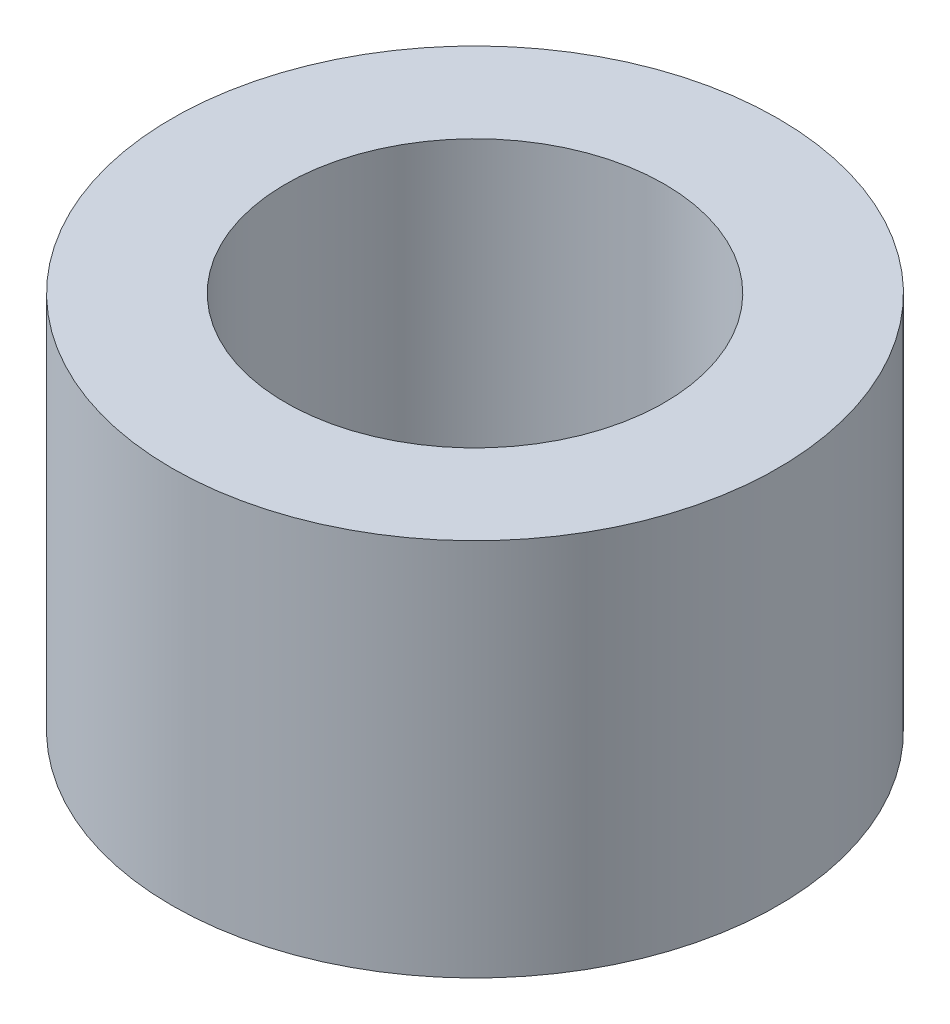
SolidWorks part; units mm, degrees
ref_plane "Front Plane" through (0, 0, 0) normal (0, 0, 1) x (1, 0, 0)
ref_plane "Top Plane" through (0, 0, 0) normal (0, 1, 0) x (1, 0, 0)
ref_plane "Right Plane" through (0, 0, 0) normal (1, 0, 0) x (0, 0, -1)
sketch "Sketch1" plane through (0, 0, 0) normal (0, 1, 0) x (1, 0, 0)
  circle A0 centre (0, 0) radius 5.08
  dimension "D1" = 10.16
extrude "Boss-Extrude1" add sketch "Sketch1" along normal blind 6.35
sketch "Sketch2" plane through (0, 0, 0) normal (0, -1, 0) x (1, 0, 0)
  circle A0 centre (0, 0) radius 3.175
  dimension "D1" = 6.35
extrude "Cut-Extrude1" cut sketch "Sketch2" against normal through all
